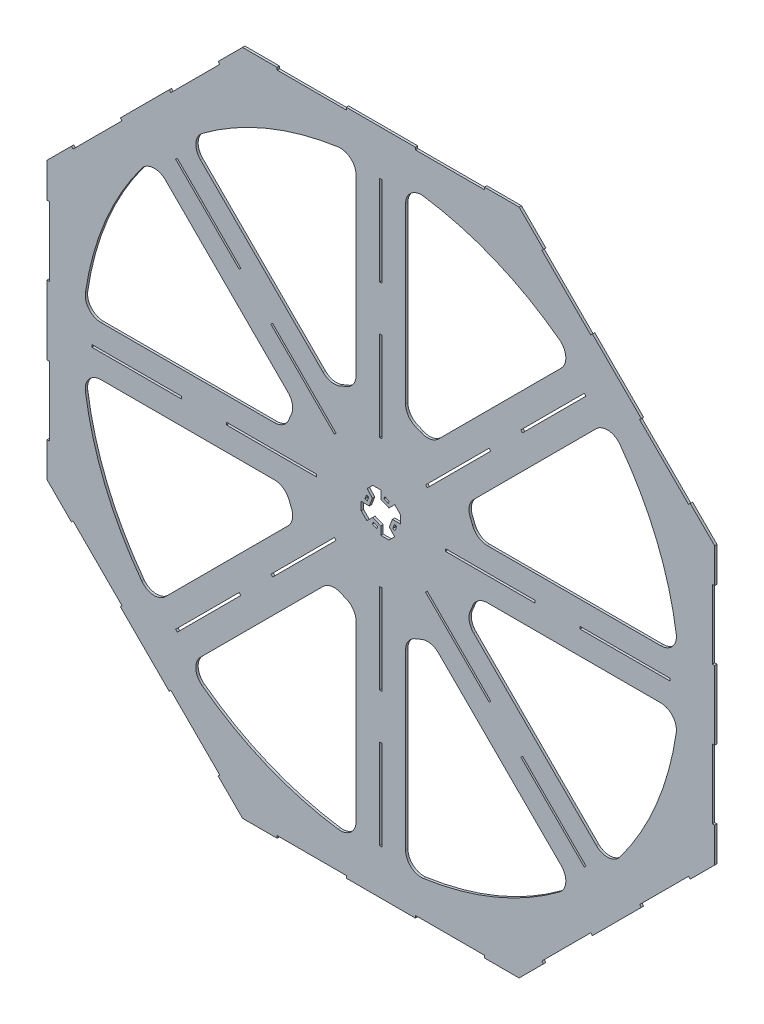
SolidWorks part; units mm, degrees
ref_plane "Plano frontal" through (0, 0, 0) normal (0, 0, 1) x (1, 0, 0)
ref_plane "Plano superior" through (0, 0, 0) normal (0, 1, 0) x (1, 0, 0)
ref_plane "Plano direito" through (0, 0, 0) normal (1, 0, 0) x (0, 0, -1)
sketch "Esboço1" plane through (0, 0, 0) normal (0, 0, 1) x (1, 0, 0)
  line L0 (-10.3553, 25) -> (0, 25)
  line L1 (17.6777, 17.6777) -> (25, 10.3553)
  line L2 (25, 10.3553) -> (25, 0)
  line L3 (17.6777, -17.6777) -> (10.3553, -25)
  line L4 (10.3553, -25) -> (0, -25)
  line L5 (180.3627, -178.2414) -> (261.1749, -259.0536)
  line L6 (-25, -10.3553) -> (-25, 0)
  line L7 (-17.4129, 17.9424) -> (-10.3553, 25)
  line L8 (-25, 10.3553) -> (25, -10.3553) construction
  line L9 (-10.3553, 25) -> (10.3553, -25) construction
  line L10 (59.1444, -57.0231) -> (139.9566, -137.8353)
  line L11 (59.1444, -57.0231) -> (57.0231, -59.1444)
  line L12 (57.0231, -59.1444) -> (137.8353, -139.9566)
  line L13 (139.9566, -137.8353) -> (137.8353, -139.9566)
  line L14 (180.3627, -178.2414) -> (178.2414, -180.3627)
  line L15 (178.2414, -180.3627) -> (259.0536, -261.1749)
  line L16 (261.1749, -259.0536) -> (259.0536, -261.1749)
  line L17 (1.5, -253.5714) -> (1.5, -367.8571)
  line L18 (-17.6777, -17.6777) -> (-10.3553, -10.3553)
  line L19 (-10.3553, -10.3553) -> (0, -14.6447)
  line L20 (0, -14.6447) -> (0, -25)
  line L21 (-9.48, -15.0475) -> (-3.9368, -17.3436)
  line L22 (-3.9368, -17.3436) -> (-5.0848, -20.1152)
  line L23 (-5.0848, -20.1152) -> (-10.6281, -17.8191)
  line L24 (-10.6281, -17.8191) -> (-9.48, -15.0475)
  line L25 (10.3553, 25) -> (-10.3553, -25) construction
  line L26 (-9.48, -15.0475) -> (-7.9493, -11.3519) construction
  line L27 (1.5, -82.1429) -> (1.5, -196.4286)
  line L28 (-14.6447, 0) -> (-25, 0)
  line L29 (-17.3966, 4.0828) -> (-20.2094, 5.1261)
  line L30 (-20.2094, 5.1261) -> (-18.1228, 10.7516)
  line L31 (-17.4129, 17.9424) -> (-10.7441, 10.5164)
  line L32 (-15.3101, 9.7083) -> (-17.3966, 4.0828)
  line L33 (-18.1228, 10.7516) -> (-15.3101, 9.7083)
  line L34 (-10.7441, 10.5164) -> (-14.6447, 0)
  line L35 (0, 14.6447) -> (0, 25)
  line L36 (3.9368, 17.3436) -> (5.0848, 20.1152)
  line L37 (5.0848, 20.1152) -> (10.6281, 17.8191)
  line L38 (17.6777, 17.6777) -> (10.3553, 10.3553)
  line L39 (9.48, 15.0475) -> (3.9368, 17.3436)
  line L40 (10.6281, 17.8191) -> (9.48, 15.0475)
  line L41 (10.3553, 10.3553) -> (0, 14.6447)
  line L42 (14.6447, 0) -> (25, 0)
  line L43 (17.3966, -4.0828) -> (20.2094, -5.1261)
  line L44 (20.2094, -5.1261) -> (18.1228, -10.7516)
  line L45 (17.6777, -17.6777) -> (10.7441, -10.5164)
  line L46 (15.3101, -9.7083) -> (17.3966, -4.0828)
  line L47 (18.1228, -10.7516) -> (15.3101, -9.7083)
  line L48 (10.7441, -10.5164) -> (14.6447, 0)
  line L49 (253.5714, 1.5) -> (367.8571, 1.5)
  line L50 (82.1429, 1.5) -> (196.4286, 1.5)
  line L51 (82.1429, 1.5) -> (82.1429, -1.5)
  line L52 (82.1429, -1.5) -> (196.4286, -1.5)
  line L53 (196.4286, 1.5) -> (196.4286, -1.5)
  line L54 (253.5714, 1.5) -> (253.5714, -1.5)
  line L55 (253.5714, -1.5) -> (367.8571, -1.5)
  line L56 (367.8571, 1.5) -> (367.8571, -1.5)
  line L57 (1.5, -82.1429) -> (-1.5, -82.1429)
  line L58 (-1.5, -82.1429) -> (-1.5, -196.4286)
  line L59 (1.5, -196.4286) -> (-1.5, -196.4286)
  line L60 (1.5, -253.5714) -> (-1.5, -253.5714)
  line L61 (-1.5, -253.5714) -> (-1.5, -367.8571)
  line L62 (1.5, -367.8571) -> (-1.5, -367.8571)
  line L63 (-178.2414, -180.3627) -> (-259.0536, -261.1749)
  line L64 (-57.0231, -59.1444) -> (-137.8353, -139.9566)
  line L65 (-57.0231, -59.1444) -> (-59.1444, -57.0231)
  line L66 (-59.1444, -57.0231) -> (-139.9566, -137.8353)
  line L67 (-137.8353, -139.9566) -> (-139.9566, -137.8353)
  line L68 (-178.2414, -180.3627) -> (-180.3627, -178.2414)
  line L69 (-180.3627, -178.2414) -> (-261.1749, -259.0536)
  line L70 (-259.0536, -261.1749) -> (-261.1749, -259.0536)
  line L71 (-253.5714, -1.5) -> (-367.8571, -1.5)
  line L72 (-82.1429, -1.5) -> (-196.4286, -1.5)
  line L73 (-82.1429, -1.5) -> (-82.1429, 1.5)
  line L74 (-82.1429, 1.5) -> (-196.4286, 1.5)
  line L75 (-196.4286, -1.5) -> (-196.4286, 1.5)
  line L76 (-253.5714, -1.5) -> (-253.5714, 1.5)
  line L77 (-253.5714, 1.5) -> (-367.8571, 1.5)
  line L78 (-367.8571, -1.5) -> (-367.8571, 1.5)
  line L79 (-180.3627, 178.2414) -> (-261.1749, 259.0536)
  line L80 (-59.1444, 57.0231) -> (-139.9566, 137.8353)
  line L81 (-59.1444, 57.0231) -> (-57.0231, 59.1444)
  line L82 (-57.0231, 59.1444) -> (-137.8353, 139.9566)
  line L83 (-139.9566, 137.8353) -> (-137.8353, 139.9566)
  line L84 (-180.3627, 178.2414) -> (-178.2414, 180.3627)
  line L85 (-178.2414, 180.3627) -> (-259.0536, 261.1749)
  line L86 (-261.1749, 259.0536) -> (-259.0536, 261.1749)
  line L87 (-1.5, 253.5714) -> (-1.5, 367.8571)
  line L88 (-1.5, 82.1429) -> (-1.5, 196.4286)
  line L89 (-1.5, 82.1429) -> (1.5, 82.1429)
  line L90 (1.5, 82.1429) -> (1.5, 196.4286)
  line L91 (-1.5, 196.4286) -> (1.5, 196.4286)
  line L92 (-1.5, 253.5714) -> (1.5, 253.5714)
  line L93 (1.5, 253.5714) -> (1.5, 367.8571)
  line L94 (-1.5, 367.8571) -> (1.5, 367.8571)
  line L95 (178.2414, 180.3627) -> (259.0536, 261.1749)
  line L96 (57.0231, 59.1444) -> (137.8353, 139.9566)
  line L97 (57.0231, 59.1444) -> (59.1444, 57.0231)
  line L98 (59.1444, 57.0231) -> (139.9566, 137.8353)
  line L99 (137.8353, 139.9566) -> (139.9566, 137.8353)
  line L100 (178.2414, 180.3627) -> (180.3627, 178.2414)
  line L101 (180.3627, 178.2414) -> (261.1749, 259.0536)
  line L102 (259.0536, 261.1749) -> (261.1749, 259.0536)
  line L103 (-176.0408, -425) -> (-132.0306, -425)
  line L104 (176.0408, -425) -> (207.1607, -393.8801)
  line L105 (425, -176.0408) -> (425, -132.0306)
  line L106 (425, 176.0408) -> (393.8801, 207.1607)
  line L107 (176.0408, 425) -> (132.0306, 425)
  line L108 (-176.0408, 425) -> (-207.1607, 393.8801)
  line L109 (-425, 176.0408) -> (-425, 132.0306)
  line L110 (-425, -176.0408) -> (-393.8801, -207.1607)
  line L111 (-44.0102, -425) -> (44.0102, -425)
  line L112 (-425, 44.0102) -> (-425, -44.0102)
  line L113 (0, 14.6447) -> (0, -14.6447) construction
  line L114 (-17.4129, 17.9424) -> (-25, 10.3553) construction
  line L115 (-25, 10.3553) -> (-25, 0) construction
  line L116 (0, 25) -> (10.3553, 25) construction
  line L117 (10.3553, 25) -> (17.6777, 17.6777) construction
  line L118 (25, 0) -> (25, -10.3553) construction
  line L119 (25, -10.3553) -> (17.6777, -17.6777) construction
  line L120 (-17.6777, -17.6777) -> (-25, -10.3553)
  line L121 (0, -25) -> (-10.3553, -25) construction
  line L122 (-132.0306, -425) -> (-132.0306, -422)
  line L123 (-132.0306, -422) -> (-44.0102, -422)
  line L124 (-44.0102, -425) -> (-44.0102, -422)
  line L125 (-425, -132.0306) -> (-425, -176.0408)
  line L126 (44.0102, -425) -> (44.0102, -422)
  line L127 (44.0102, -422) -> (132.0306, -422)
  line L128 (132.0306, -425) -> (132.0306, -422)
  line L129 (-393.8801, -207.1607) -> (-391.7588, -205.0393)
  line L130 (-391.7588, -205.0393) -> (-329.519, -267.2792)
  line L131 (-331.6403, -269.4005) -> (-329.519, -267.2792)
  line L132 (132.0306, -425) -> (176.0408, -425)
  line L133 (-269.4005, -331.6403) -> (-267.2792, -329.519)
  line L134 (-267.2792, -329.519) -> (-205.0393, -391.7588)
  line L135 (-207.1607, -393.8801) -> (-205.0393, -391.7588)
  line L136 (-393.8801, 207.1607) -> (-425, 176.0408)
  line L137 (-425, 132.0306) -> (-422, 132.0306)
  line L138 (-422, 132.0306) -> (-422, 44.0102)
  line L139 (-425, 44.0102) -> (-422, 44.0102)
  line L140 (-269.4005, 331.6403) -> (-331.6403, 269.4005)
  line L141 (-425, -44.0102) -> (-422, -44.0102)
  line L142 (-422, -44.0102) -> (-422, -132.0306)
  line L143 (-425, -132.0306) -> (-422, -132.0306)
  line L144 (-132.0306, 425) -> (-176.0408, 425)
  line L145 (-207.1607, 393.8801) -> (-205.0393, 391.7588)
  line L146 (-205.0393, 391.7588) -> (-267.2792, 329.519)
  line L147 (-269.4005, 331.6403) -> (-267.2792, 329.519)
  line L148 (44.0102, 425) -> (-44.0102, 425)
  line L149 (-331.6403, 269.4005) -> (-329.519, 267.2792)
  line L150 (-329.519, 267.2792) -> (-391.7588, 205.0393)
  line L151 (-393.8801, 207.1607) -> (-391.7588, 205.0393)
  line L152 (207.1607, 393.8801) -> (176.0408, 425)
  line L153 (132.0306, 425) -> (132.0306, 422)
  line L154 (132.0306, 422) -> (44.0102, 422)
  line L155 (44.0102, 425) -> (44.0102, 422)
  line L156 (331.6403, 269.4005) -> (269.4005, 331.6403)
  line L157 (-44.0102, 425) -> (-44.0102, 422)
  line L158 (-44.0102, 422) -> (-132.0306, 422)
  line L159 (-132.0306, 425) -> (-132.0306, 422)
  line L160 (425, 132.0306) -> (425, 176.0408)
  line L161 (393.8801, 207.1607) -> (391.7588, 205.0393)
  line L162 (391.7588, 205.0393) -> (329.519, 267.2792)
  line L163 (331.6403, 269.4005) -> (329.519, 267.2792)
  line L164 (425, -44.0102) -> (425, 44.0102)
  line L165 (269.4005, 331.6403) -> (267.2792, 329.519)
  line L166 (267.2792, 329.519) -> (205.0393, 391.7588)
  line L167 (207.1607, 393.8801) -> (205.0393, 391.7588)
  line L168 (393.8801, -207.1607) -> (425, -176.0408)
  line L169 (425, -132.0306) -> (422, -132.0306)
  line L170 (-10.3553, -25) -> (-17.6777, -17.6777) construction
  line L171 (422, -132.0306) -> (422, -44.0102)
  line L172 (425, -44.0102) -> (422, -44.0102)
  line L173 (269.4005, -331.6403) -> (331.6403, -269.4005)
  line L174 (425, 44.0102) -> (422, 44.0102)
  line L175 (422, 44.0102) -> (422, 132.0306)
  line L176 (425, 132.0306) -> (422, 132.0306)
  line L178 (207.1607, -393.8801) -> (205.0393, -391.7588)
  line L179 (205.0393, -391.7588) -> (267.2792, -329.519)
  line L180 (269.4005, -331.6403) -> (267.2792, -329.519)
  line L182 (331.6403, -269.4005) -> (329.519, -267.2792)
  line L183 (329.519, -267.2792) -> (391.7588, -205.0393)
  line L184 (393.8801, -207.1607) -> (391.7588, -205.0393)
  line L185 (-331.6403, -269.4005) -> (-269.4005, -331.6403)
  line L187 (-207.1607, -393.8801) -> (-176.0408, -425)
  point P21 (-5.1777, -12.5)
  point P28 (-6.7084, -16.1955)
  point P29 (-7.8565, -18.9672)
  point P61 (0, 0)
  point P65 (7.8565, 18.9672)
  point P68 (82.1429, 0)
  point P114 (0, 0)
  point P125 (0, 0)
  point P128 (0, 0)
  point P191 (0, 0)
  point P192 (-19.1661, 7.9389)
  point P193 (0, 0)
  point P194 (-12.6944, 5.2582)
  point P195 (0, 0)
  point P196 (12.6944, -5.2582)
  point P201 (19.1661, -7.9389)
  dimension "D3" = 3
  dimension "D4" = 114.2857
  dimension "D5" = 3
  dimension "D6" = 6
  dimension "D7" = 4
  dimension "D8" = 3
  dimension "D9" = 57.1429
  dimension "D11" = 57.1429
  dimension "D13" = 352.0815
  dimension "D10" = 3
  dimension "D18" = 3
  dimension "D19" = 6
  dimension "D20" = 6
  dimension "D21" = 22.5
  dimension "D22" = 22.5
  dimension "D23" = 67.5
  dimension "D24" = 25
  dimension "D25" = 25
  dimension "D26" = 50
  dimension "D27" = 135
  dimension "D28" = 135
  dimension "D29" = 4
  dimension "D30" = 4
  dimension "D31" = 6
  dimension "D32" = 4
  dimension "D33" = 114.2857
  dimension "D34" = 88.0204
  dimension "D12" = 8
  dimension "D16" = 44.0102
  dimension "D17" = 88.0204
  dimension "D35" = 88.0204
  dimension "D36" = 3
  dimension "D37" = 8
extrude "Ressalto-extrusão1" add sketch "Esboço1" along normal blind 3
sketch "Esboço2" plane through (0, 0, 0) normal (0, 0, -1) x (-1, 0, 0)
  line L0 (31.5, 120.9659) -> (31.5, 378.6922)
  line L1 (63.2619, 107.8097) -> (245.5019, 290.0497)
  line L2 (1.5, 367.8571) -> (1.5, 253.5714) construction
  line L3 (57.0231, 59.1444) -> (137.8353, 139.9566) construction
  line L4 (178.2414, 180.3627) -> (259.0536, 261.1749) construction
  line L5 (107.8097, 63.2619) -> (290.0497, 245.5019)
  line L6 (120.9659, 31.5) -> (378.6922, 31.5)
  line L7 (120.9659, -31.5) -> (378.6922, -31.5)
  line L8 (107.8097, -63.2619) -> (290.0497, -245.5019)
  line L9 (63.2619, -107.8097) -> (245.5019, -290.0497)
  line L10 (31.5, -120.9659) -> (31.5, -378.6922)
  line L11 (-31.5, -120.9659) -> (-31.5, -378.6922)
  line L12 (-63.2619, -107.8097) -> (-245.5019, -290.0497)
  line L13 (-107.8097, -63.2619) -> (-290.0497, -245.5019)
  line L14 (-120.9659, -31.5) -> (-378.6922, -31.5)
  line L15 (-120.9659, 31.5) -> (-378.6922, 31.5)
  line L16 (-107.8097, 63.2619) -> (-290.0497, 245.5019)
  line L17 (-63.2619, 107.8097) -> (-245.5019, 290.0497)
  line L18 (-31.5, 120.9659) -> (-31.5, 378.6922)
  circle A0 centre (0, 0) radius 380
  circle A1 centre (0, 0) radius 125
  point P44 (0, 0)
  dimension "D1" = 760
  dimension "D2" = 250
  dimension "D3" = 30
  dimension "D4" = 30
  dimension "D5" = 8
extrude "Corte-extrusão1" cut sketch "Esboço2" against normal through all both and the other way through all contours A1 L18 A0 L17 | A1 L1 A0 L0 | A1 L6 A0 L5 | A1 L8 A0 L7 | A1 L10 A0 L9 | A1 L12 A0 L11 | A1 L14 A0 L13 | A1 L16 A0 L15
fillet "Filete1" radius 20 32 edges at (-31.5, 120.9659, 1.5) (-63.2619, 107.8097, 1.5) (-245.5019, 290.0497, 1.5) (-31.5, 378.6922, 1.5) (-290.0497, -245.5019, 1.5) (-378.6922, -31.5, 1.5) (-378.6922, 31.5, 1.5) (-290.0497, 245.5019, 1.5) (-107.8097, -63.2619, 1.5) (-120.9659, -31.5, 1.5) (-120.9659, 31.5, 1.5) (-107.8097, 63.2619, 1.5) (-245.5019, -290.0497, 1.5) (-63.2619, -107.8097, 1.5) (-31.5, -120.9659, 1.5) (31.5, -120.9659, 1.5) (63.2619, -107.8097, 1.5) (-31.5, -378.6922, 1.5) (31.5, -378.6922, 1.5) (245.5019, -290.0497, 1.5) (290.0497, -245.5019, 1.5) (107.8097, -63.2619, 1.5) (120.9659, -31.5, 1.5) (378.6922, -31.5, 1.5) (378.6922, 31.5, 1.5) (290.0497, 245.5019, 1.5) (107.8097, 63.2619, 1.5) (120.9659, 31.5, 1.5) (245.5019, 290.0497, 1.5) (63.2619, 107.8097, 1.5) (31.5, 120.9659, 1.5) (31.5, 378.6922, 1.5)
sketch "Esboço3" plane through (0, 0, 3) normal (0, 0, 1) x (1, 0, 0)
  line L0 (0, 25) -> (17.6777, 17.6777) construction
  line L1 (5.6282, 22.6687) -> (4.4802, 19.8971) construction
  line L2 (4.4802, 19.8971) -> (10.7531, 17.2988) construction
  line L3 (10.7531, 17.2988) -> (11.9011, 20.0704) construction
  line L7 (10.3553, 10.3553) -> (0, 14.6447) construction
  line L8 (0, 14.6447) -> (10.3553, 10.3553)
  point P6 (7.7767, 11.4234)
  point P9 (5.1777, 12.5)
  point P10 (0, 0)
  point P18 (0, 0)
  dimension "D1" = 3
  dimension "D2" = 9.5671
  dimension "D3" = 13.5299
